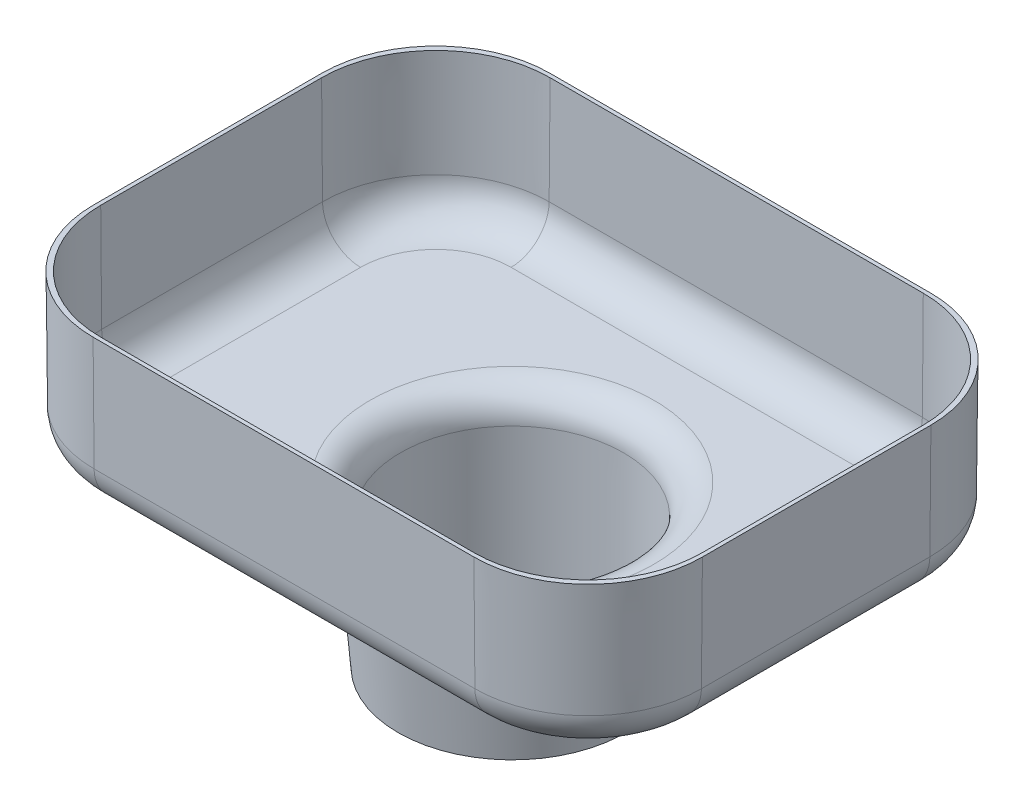
SolidWorks part; units mm, degrees
ref_plane "Front Plane" through (0, 0, 0) normal (0, 0, 1) x (1, 0, 0)
ref_plane "Top Plane" through (0, 0, 0) normal (0, 1, 0) x (1, 0, 0)
ref_plane "Right Plane" through (0, 0, 0) normal (1, 0, 0) x (0, 0, -1)
sketch "Sketch5" plane through (0, 0, 0) normal (0, 1, 0) x (1, 0, 0)
  line L1 (-26.5686, 32.366) -> (36.9314, 32.366)
  line L2 (-45.6186, 13.316) -> (-45.6186, -24.784)
  line L3 (-26.5686, -43.834) -> (36.9314, -43.834)
  line L4 (55.9814, 13.316) -> (55.9814, -24.784)
  arc A0 (36.9314, 32.366) -> (55.9814, 13.316) centre (36.9314, 13.316) cw
  arc A1 (36.9314, -43.834) -> (55.9814, -24.784) centre (36.9314, -24.784) ccw
  arc A2 (-45.6186, -24.784) -> (-26.5686, -43.834) centre (-26.5686, -24.784) ccw
  arc A3 (-26.5686, 32.366) -> (-45.6186, 13.316) centre (-26.5686, 13.316) ccw
  point P6 (55.9814, 32.366)
  point P11 (-45.6186, -43.834)
  point P14 (-45.6186, 32.366)
  dimension "D3" = 19.05
  dimension "D1" = 101.6
  dimension "D2" = 76.2
extrude "Boss-Extrude2" add sketch "Sketch5" against normal blind 25.4 draft 0.5
sketch "Sketch6" plane through (0, 0, 0) normal (0, 1, 0) x (1, 0, 0)
  line L0 (5.1814, 32.366) -> (5.1814, -43.834) construction
  line L1 (-25.9336, 31.731) -> (36.2964, 31.731)
  line L2 (-44.9836, 12.681) -> (-44.9836, -24.149)
  line L3 (-25.9336, -43.199) -> (36.2964, -43.199)
  line L4 (55.3464, 12.681) -> (55.3464, -24.149)
  line L5 (36.9314, 32.366) -> (-26.5686, 32.366) construction
  line L6 (-26.5686, -43.834) -> (36.9314, -43.834) construction
  line L7 (-45.6186, -5.734) -> (55.9814, -5.734) construction
  line L8 (-45.6186, 13.316) -> (-45.6186, -24.784) construction
  line L9 (55.9814, -24.784) -> (55.9814, 13.316) construction
  arc A0 (-44.9836, -24.149) -> (-25.9336, -43.199) centre (-25.9336, -24.149) ccw
  arc A1 (36.2964, -43.199) -> (55.3464, -24.149) centre (36.2964, -24.149) ccw
  arc A2 (36.2964, 31.731) -> (55.3464, 12.681) centre (36.2964, 12.681) cw
  arc A3 (-25.9336, 31.731) -> (-44.9836, 12.681) centre (-25.9336, 12.681) ccw
  point P24 (-24.8783, 30.2605)
  dimension "D1" = 19.05
  dimension "D2" = 74.93
  dimension "D3" = 100.33
extrude "Cut-Extrude1" cut sketch "Sketch6" against normal blind 24.13 draft 0.5
fillet "Fillet1" radius 6.35 8 edges at (5.1814, -25.4, -32.1444) (-39.8822, -25.4, -26.6297) (-45.3969, -25.4, 5.734) (-39.8822, -25.4, 38.0976) (5.1814, -25.4, 43.6123) (50.245, -25.4, 38.0976) (55.7597, -25.4, 5.734) (50.245, -25.4, -26.6297)
fillet "Fillet2" radius 6.35 8 edges at (55.1358, -24.13, 5.734) (49.6179, -24.13, 37.4705) (5.1814, -24.13, 42.9884) (-39.2551, -24.13, 37.4705) (-44.773, -24.13, 5.734) (-39.2551, -24.13, -26.0025) (5.1814, -24.13, -31.5205) (49.6179, -24.13, -26.0025)
sketch "Sketch7" plane through (0, -25.4, 0) normal (0, -1, 0) x (1, 0, 0)
  line L0 (5.1814, 43.6672) -> (5.1814, -32.1993) construction
  line L1 (-26.5686, 43.6672) -> (36.9314, 43.6672) construction
  line L2 (36.9314, -32.1993) -> (-26.5686, -32.1993) construction
  circle A0 centre (5.1814, 5.734) radius 21.209
  dimension "D1" = 42.418
extrude "Boss-Extrude3" add sketch "Sketch7" along normal blind 25.4 draft 5
sketch "Sketch11" plane through (0, -50.8, 0) normal (0, -1, 0) x (1, 0, 0)
  circle A0 centre (5.1814, 5.734) radius 18.415
  dimension "D1" = 36.83
extrude "Cut-Extrude2" cut sketch "Sketch11" against normal up to next (26.67 mm away) draft 0.5 draft outward yes
fillet "Fillet3" radius 5.08 1 edges at (5.1814, -24.13, 24.3817)
fillet "Fillet4" radius 5.08 1 edges at (5.1814, -25.4, -15.475)
